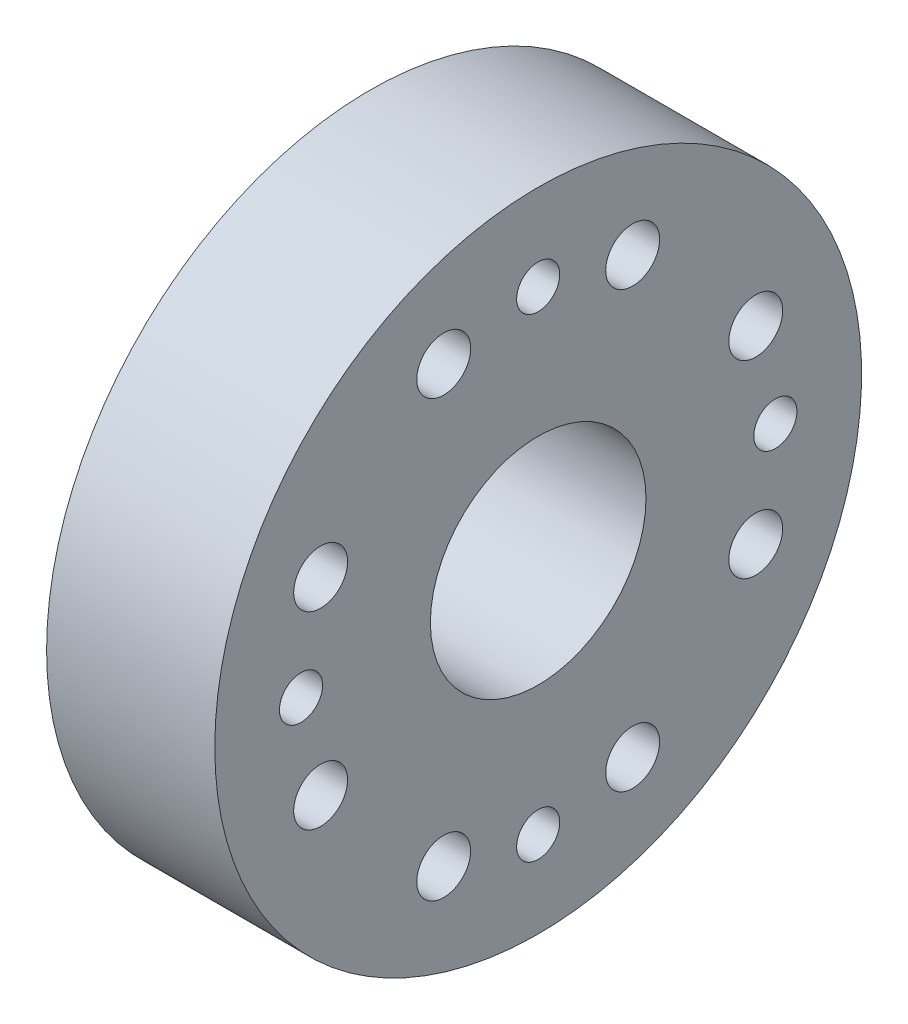
SolidWorks part; units mm, degrees
ref_plane "Front Plane" through (0, 0, 0) normal (0, 0, 1) x (1, 0, 0)
ref_plane "Top Plane" through (0, 0, 0) normal (0, 1, 0) x (1, 0, 0)
ref_plane "Right Plane" through (0, 0, 0) normal (1, 0, 0) x (0, 0, -1)
sketch "Sketch1" plane through (0, 0, 0) normal (0, 0, 1) x (1, 0, 0)
  line L0 (6.6094, 15) -> (1.1906, 15)
  line L1 (0, 0) -> (7.8, 0)
  line L2 (0, 0) -> (0, 14)
  line L3 (7.8, 14) -> (7.8, 15)
  line L4 (7.8, 0) -> (7.8, 14)
  line L5 (0, 15) -> (0, 14)
  line L10 (1.1906, 15) -> (0, 15)
  line L14 (7.8, 15) -> (6.6094, 15)
  dimension "D1" = 7.8
  dimension "D2" = 15
  dimension "D5" = 1.1906
revolve "Revolve1" add sketch "Sketch1" angle 360 about L1
sketch "Sketch4" plane through (7.8, 0, 0) normal (1, 0, 0) x (0, 0, -1)
  line L0 (0, -23.8998) -> (0, 29.2964) construction
  line L1 (31.7409, 0) -> (-31.7451, 0) construction
  line L2 (0, 0) -> (18.9307, 32.789) construction
  line L3 (0, 0) -> (-17.3596, 30.0677) construction
  circle A0 centre (0, 11) radius 1
  circle A1 centre (-4.3818, 10.0896) radius 1.25
  circle A2 centre (4.3818, 10.0896) radius 1.25
  circle A3 centre (10.0896, -4.3818) radius 1.25
  circle A4 centre (11, 0) radius 1
  circle A5 centre (10.0896, 4.3818) radius 1.25
  circle A6 centre (-4.3818, -10.0896) radius 1.25
  circle A7 centre (0, -11) radius 1
  circle A8 centre (4.3818, -10.0896) radius 1.25
  circle A9 centre (-10.0896, 4.3818) radius 1.25
  circle A10 centre (-11, 0) radius 1
  circle A11 centre (-10.0896, -4.3818) radius 1.25
  dimension "D1" = 2
  dimension "D5" = 2.5
  dimension "D2" = 11
  dimension "D4" = 30
  dimension "D6" = 11
extrude "Extrude2" cut sketch "Sketch4" against normal through all
sketch "Sketch5" plane through (7.8, 0, 0) normal (1, 0, 0) x (0, 0, -1)
  circle A0 centre (0, 0) radius 5
  dimension "D1" = 10
extrude "Cut-Extrude1" cut sketch "Sketch5" against normal through all
